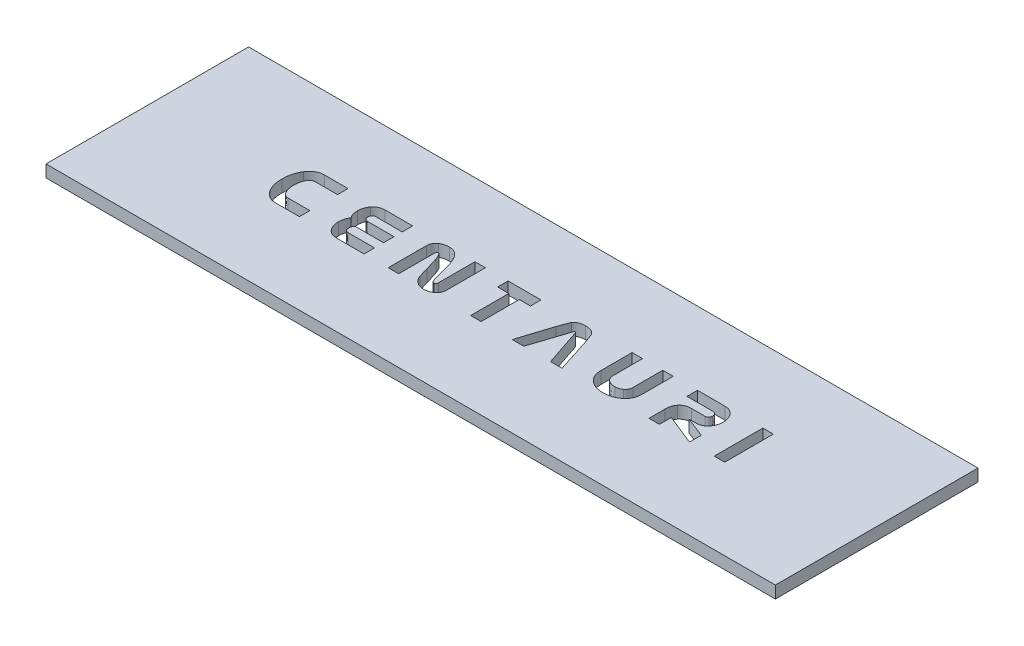
SolidWorks part; units mm, degrees
ref_plane "Front Plane" through (0, 0, 0) normal (0, 0, 1) x (1, 0, 0)
ref_plane "Top Plane" through (0, 0, 0) normal (0, 1, 0) x (1, 0, 0)
ref_plane "Right Plane" through (0, 0, 0) normal (1, 0, 0) x (0, 0, -1)
sketch "Sketch1" plane through (0, 0, 0) normal (0, 1, 0) x (1, 0, 0)
  line L1 (-34.6939, 31.3776) -> (145.3061, 31.3776)
  line L2 (-34.6939, 31.3776) -> (-34.6939, -18.6224)
  line L3 (-34.6939, -18.6224) -> (145.3061, -18.6224)
  line L4 (145.3061, 31.3776) -> (145.3061, -18.6224)
  dimension "D1" = 50
  dimension "D2" = 180
extrude "Boss-Extrude1" add sketch "Sketch1" along normal blind 3
sketch "Sketch3" plane through (0, 3, 0) normal (0, 1, 0) x (1, 0, 0)
  line L0 (145.3061, 1.3776) -> (-34.6939, 1.3776) construction
  line L1 (145.3061, -18.6224) -> (145.3061, 31.3776) construction
  line L2 (-34.6939, 31.3776) -> (-34.6939, -18.6224) construction
  line L3 (-34.6939, -18.6224) -> (145.3061, -18.6224) construction
  text T0 "CENTAURI" font "Nasa" height 12
  dimension "D1" = 20
extrude "Cut-Extrude2" cut sketch "Sketch3" against normal through all
